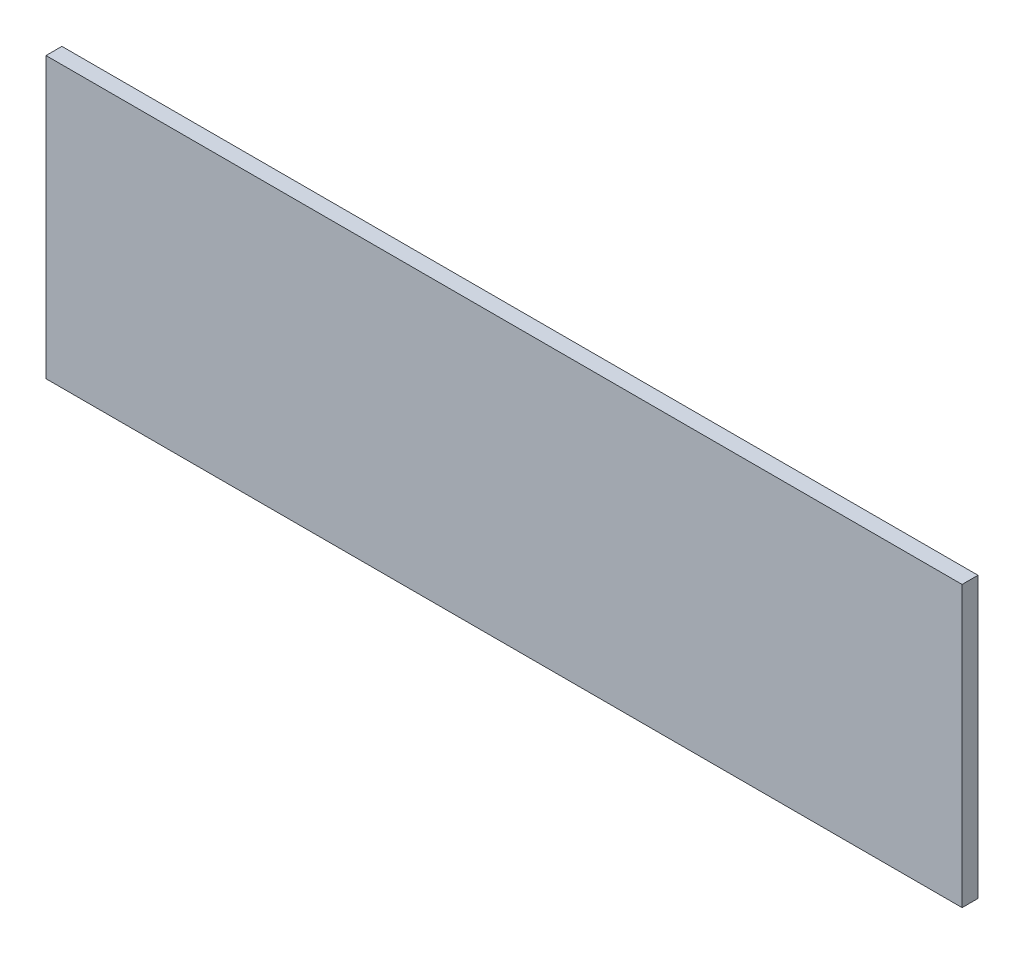
SolidWorks part; units mm, degrees
ref_plane "Front Plane" through (0, 0, 0) normal (0, 0, 1) x (1, 0, 0)
ref_plane "Top Plane" through (0, 0, 0) normal (0, 1, 0) x (1, 0, 0)
ref_plane "Right Plane" through (0, 0, 0) normal (1, 0, 0) x (0, 0, -1)
sketch "Sketch1" plane through (0, 0, 0) normal (0, 0, 1) x (1, 0, 0)
  line L1 (-360, 110) -> (360, 110)
  line L2 (-360, 110) -> (-360, -110)
  line L3 (-360, -110) -> (360, -110)
  line L4 (360, 110) -> (360, -110)
  line L5 (-360, 110) -> (360, -110) construction
  line L6 (-360, -110) -> (360, 110) construction
  point P0 (0, 0)
  dimension "D1" = 720
  dimension "D2" = 220
extrude "Boss-Extrude1" add sketch "Sketch1" along normal blind 12.5
